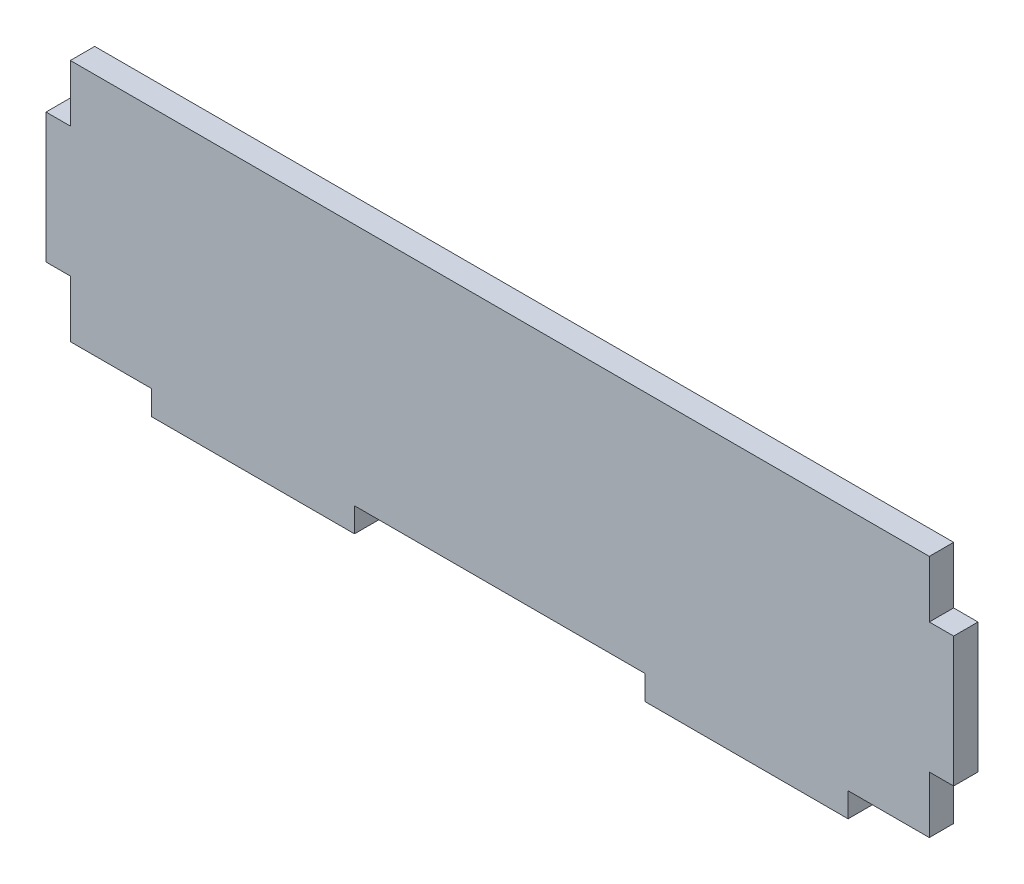
SolidWorks part; units mm, degrees
ref_plane "前视基准面" through (0, 0, 0) normal (0, 0, 1) x (1, 0, 0)
ref_plane "上视基准面" through (0, 0, 0) normal (0, 1, 0) x (1, 0, 0)
ref_plane "右视基准面" through (0, 0, 0) normal (1, 0, 0) x (0, 0, -1)
sketch "草图2" plane through (0, 0, 0) normal (0, 0, 1) x (1, 0, 0)
  line L0 (59.4, 0) -> (77.3, 0)
  line L1 (6.5, 0) -> (16.5, 0)
  line L3 (6.5, 30) -> (112.3, 30)
  line L5 (59.4, 0) -> (41.5, 0)
  line L7 (77.3, 0) -> (77.3, -3)
  line L8 (77.3, -3) -> (102.3, -3)
  line L9 (102.3, 0) -> (102.3, -3)
  line L10 (102.3, 0) -> (112.3, 0)
  line L12 (41.5, 0) -> (41.5, -3)
  line L13 (41.5, -3) -> (16.5, -3)
  line L14 (16.5, 0) -> (16.5, -3)
  line L39 (41.5, 0) -> (77.3, 0)
  line L40 (6.5, 23) -> (6.5, 30)
  line L45 (6.5, 7) -> (3.5, 7)
  line L46 (102.3, 0) -> (112.3, 0)
  line L51 (16.5, 0) -> (6.5, 0)
  line L52 (59.4, 0) -> (41.5, 0)
  line L53 (59.4, 0) -> (77.3, 0)
  line L55 (6.5, 23) -> (3.5, 23)
  line L56 (3.5, 7) -> (3.5, 23)
  line L57 (112.3, 7) -> (112.3, 0)
  line L58 (112.3, 23) -> (112.3, 30)
  line L69 (112.3, 30) -> (112.3, 23)
  line L73 (112.3, 23) -> (115.3, 23)
  line L75 (112.3, 7) -> (115.3, 7)
  line L76 (115.3, 23) -> (115.3, 7)
  line L79 (6.5, 7) -> (6.5, 0)
extrude "凸台-拉伸1" add sketch "草图2" along normal blind 3
